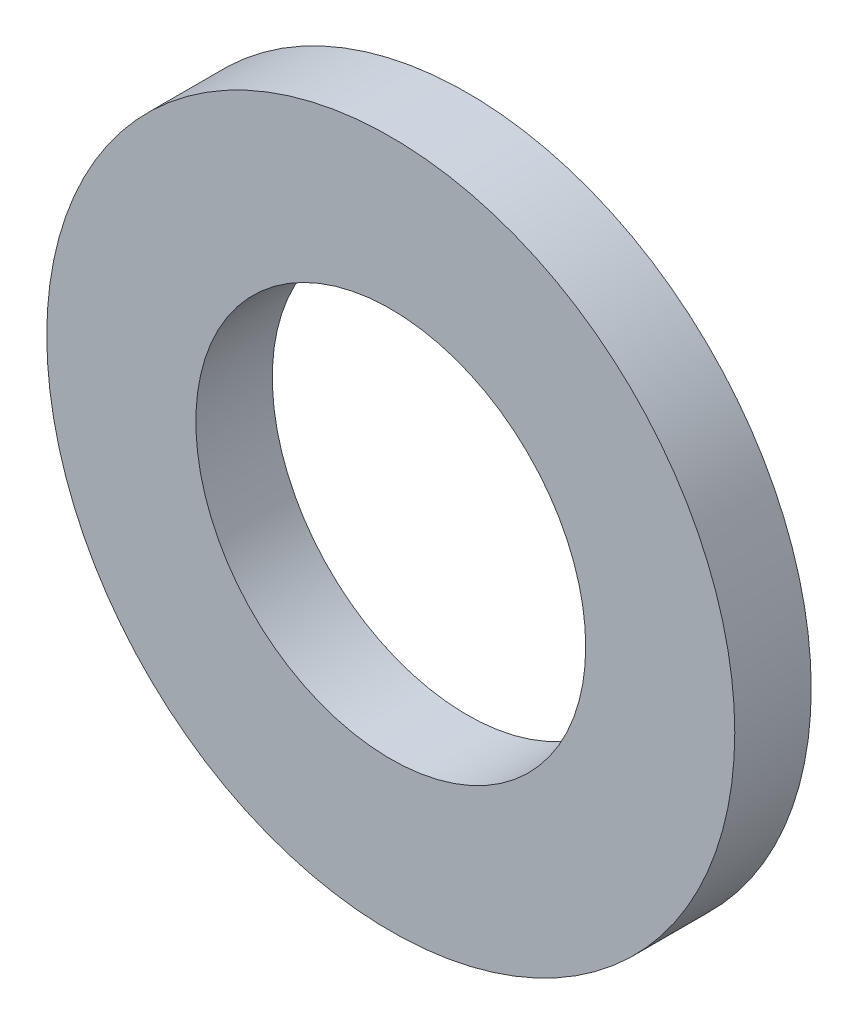
SolidWorks part; units mm, degrees
material "AISI 1010 Steel, hot rolled bar"
ref_plane "Plan de face" through (0, 0, 0) normal (0, 0, 1) x (1, 0, 0)
ref_plane "Plan de dessus" through (0, 0, 0) normal (0, 1, 0) x (1, 0, 0)
ref_plane "Plan de droite" through (0, 0, 0) normal (1, 0, 0) x (0, 0, -1)
sketch "Sketch1" plane through (0, 0, 0) normal (0, 0, 1) x (1, 0, 0)
  circle A0 centre (0, 0) radius 5.1
  circle A1 centre (0, 0) radius 9
  dimension "D1" = 10.2
  dimension "D2" = 18
extrude "Boss-Extrude1" add sketch "Sketch1" along normal blind 2
